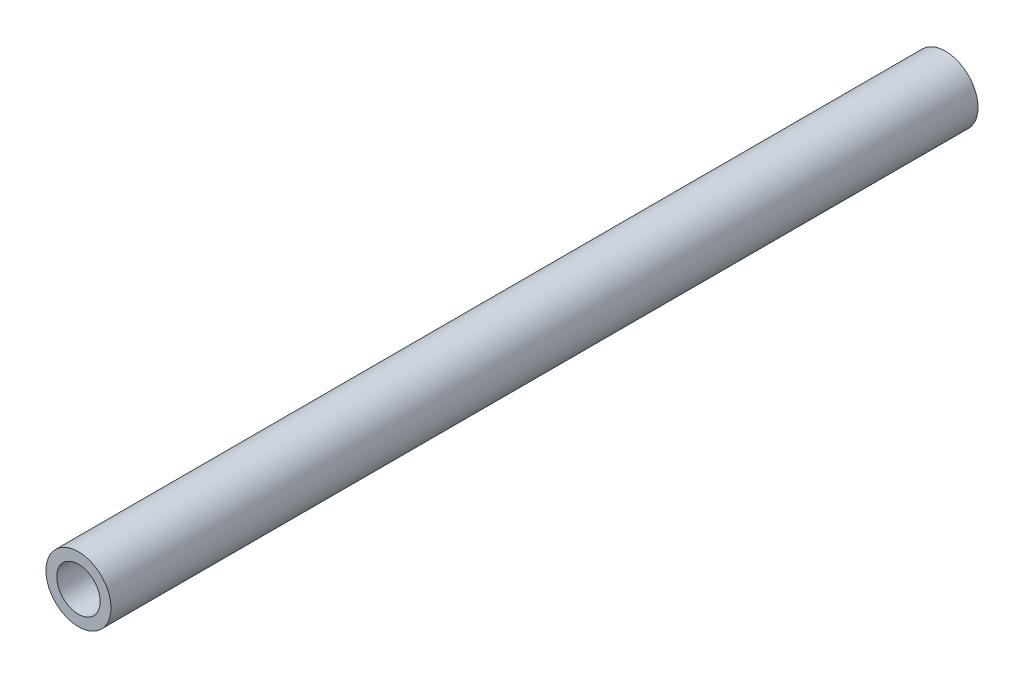
SolidWorks part; units mm, degrees
material "PVC Rigid"
ref_plane "Front Plane" through (0, 0, 0) normal (0, 0, 1) x (1, 0, 0)
ref_plane "Top Plane" through (0, 0, 0) normal (0, 1, 0) x (1, 0, 0)
ref_plane "Right Plane" through (0, 0, 0) normal (1, 0, 0) x (0, 0, -1)
sketch "Sketch1" plane through (0, 0, 0) normal (0, 0, 1) x (1, 0, 0)
  circle A0 centre (0, 0) radius 7.62
  circle A2 centre (0, 0) radius 5.08
  dimension "D1" = 15.24
  dimension "D2" = 10.16
extrude "Boss-Extrude1" add sketch "Sketch1" along normal blind 203.2
